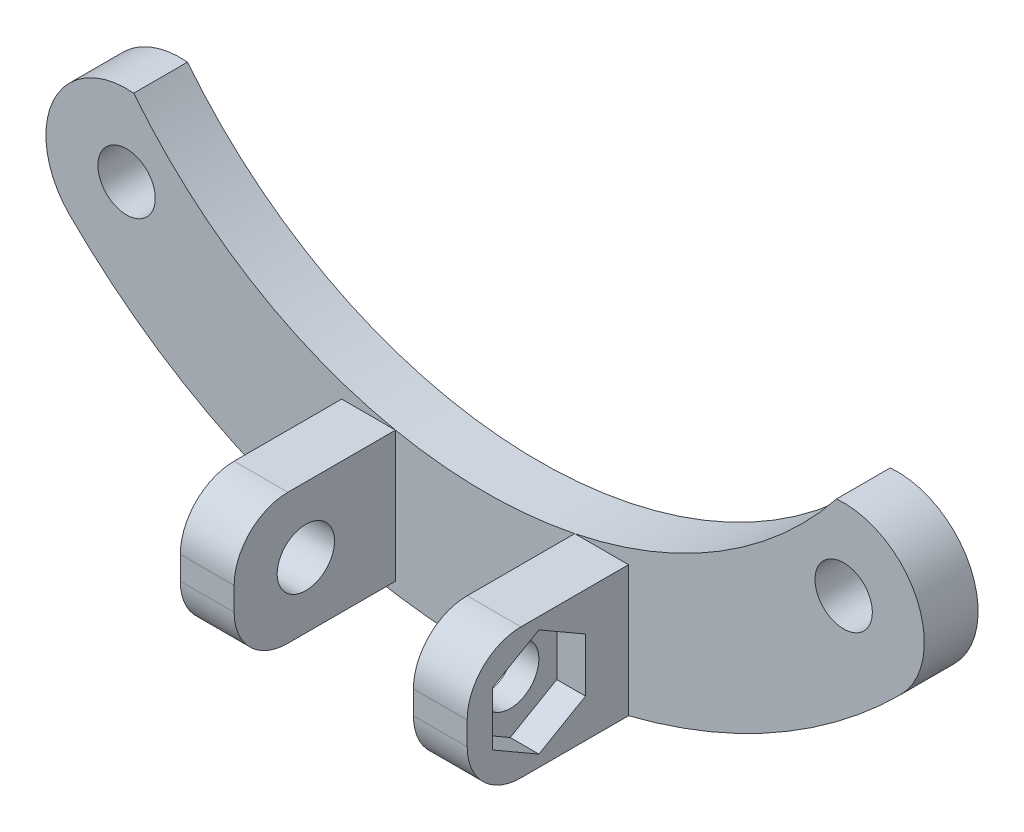
SolidWorks part; units mm, degrees
ref_plane "Alzado" through (0, 0, 0) normal (0, 0, 1) x (1, 0, 0)
ref_plane "Planta" through (0, 0, 0) normal (0, 1, 0) x (1, 0, 0)
ref_plane "Vista lateral" through (0, 0, 0) normal (1, 0, 0) x (0, 0, -1)
sketch "Croquis1" plane through (0, 0, 0) normal (0, 0, 1) x (1, 0, 0)
  line L0 (0, 0) -> (20, 20) construction
  line L1 (20, 20) -> (40, 0) construction
  line L2 (12, -9) -> (28, -9) construction
  circle A0 centre (0, 0) radius 1.6
  arc A1 (0.399, 4.4823) -> (-3.182, -3.182) centre (0, 0) ccw
  arc A2 (43.182, -3.182) -> (39.601, 4.4823) centre (40, 0) ccw
  circle A3 centre (40, 0) radius 1.6
  arc A4 (0.399, 4.4823) -> (39.601, 4.4823) centre (20, 20) ccw
  arc A5 (-3.182, -3.182) -> (43.182, -3.182) centre (20, 20) ccw
  dimension "D1" = 3.2
  dimension "D2" = 9
  dimension "D4" = 50
  dimension "D5" = 40
  dimension "D6" = 20
  dimension "D7" = 20
  dimension "D8" = 16
  dimension "D10" = 29
  dimension "D3" = 2
extrude "Saliente-Extruir1" add sketch "Croquis1" along normal blind 3
sketch "Croquis2" plane through (0, 0, 3) normal (0, 0, 1) x (1, 0, 0)
  line L1 (12, -11.7932) -> (15, -11.7932)
  line L2 (12, -11.7932) -> (12, -4.4949)
  line L3 (12, -4.4949) -> (15, -4.4949)
  line L4 (15, -11.7932) -> (15, -4.4949)
  line L5 (28, -11.7932) -> (25, -11.7932)
  line L6 (28, -11.7932) -> (28, -4.4949)
  line L7 (28, -4.4949) -> (25, -4.4949)
  line L8 (25, -11.7932) -> (25, -4.4949)
  arc A0 (-3.182, -3.182) -> (43.182, -3.182) centre (20, 20) ccw construction
  arc A1 (0.399, 4.4823) -> (39.601, 4.4823) centre (20, 20) ccw construction
  dimension "D1" = 3
  dimension "D2" = 3
extrude "Saliente-Extruir2" add sketch "Croquis2" along normal blind 9
sketch "Croquis3" plane through (12, 0, 0) normal (-1, 0, 0) x (0, 0, 1)
  line L0 (12, -4.4949) -> (3, -4.4949) construction
  line L2 (3, -4.4949) -> (3, -11.7932) construction
  circle A0 centre (8, -8.1449) radius 1.6
  dimension "D1" = 3.2
  dimension "D2" = 3.65
  dimension "D3" = 5
extrude "Cortar-Extruir1" cut sketch "Croquis3" against normal up to surface (16 mm away) up to face at (28, -8.1441, 7.5)
sketch "Croquis4" plane through (28, 0, 0) normal (1, 0, 0) x (0, 0, -1)
  line L1 (-5.4019, -9.6449) -> (-5.4019, -6.6449)
  line L2 (-5.4019, -6.6449) -> (-8, -5.1449)
  line L3 (-8, -5.1449) -> (-10.5981, -6.6449)
  line L4 (-10.5981, -6.6449) -> (-10.5981, -9.6449)
  line L5 (-10.5981, -9.6449) -> (-8, -11.1449)
  line L6 (-8, -11.1449) -> (-5.4019, -9.6449)
  circle A0 centre (-8, -8.1449) radius 2.5981 construction
  dimension "D1" = 6
extrude "Cortar-Extruir2" cut sketch "Croquis4" against normal blind 1.6
fillet "Redondeo1" radius 3 4 edges at (26.5, -11.7932, 12) (26.5, -4.4949, 12) (13.5, -4.4949, 12) (13.5, -11.7932, 12)
